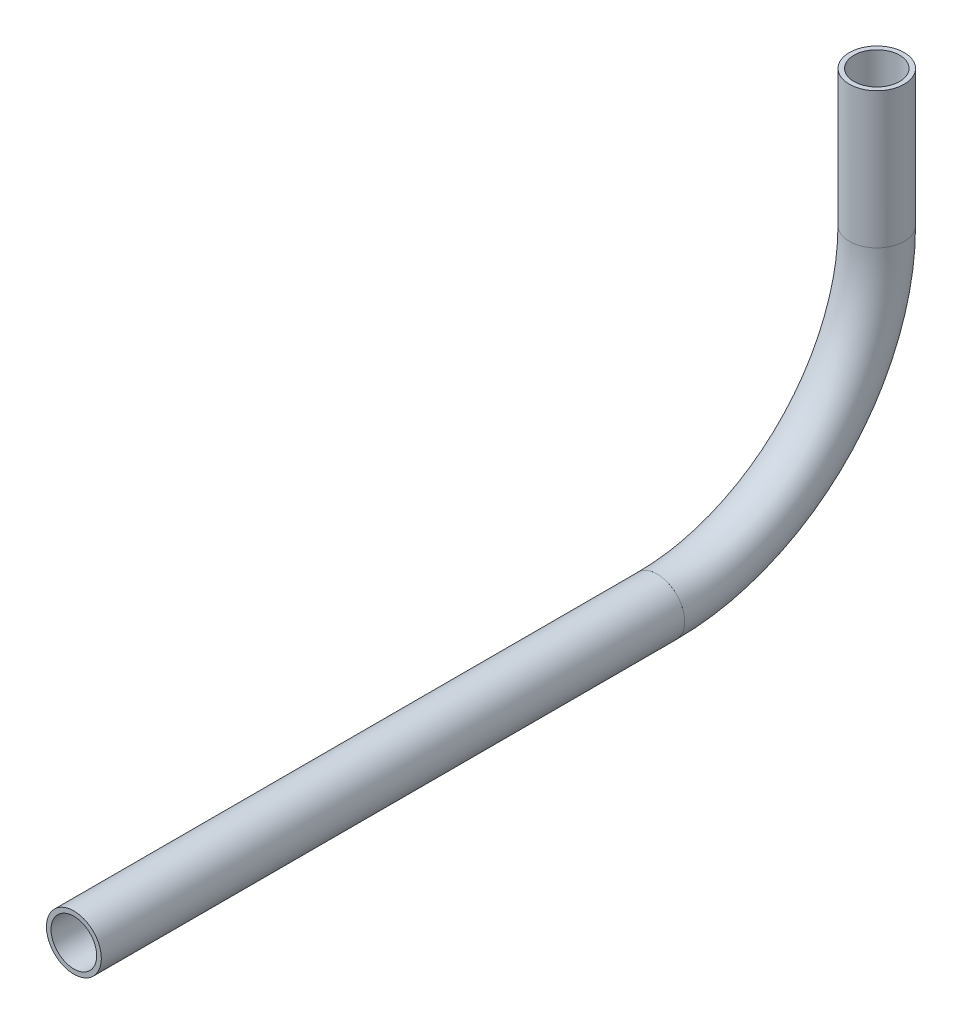
SolidWorks part; units mm, degrees
ref_plane "Front Plane" through (0, 0, 0) normal (0, 0, 1) x (1, 0, 0)
ref_plane "Top Plane" through (0, 0, 0) normal (0, 1, 0) x (1, 0, 0)
ref_plane "Right Plane" through (0, 0, 0) normal (1, 0, 0) x (0, 0, -1)
sketch "Sketch1" plane through (0, 0, 0) normal (1, 0, 0) x (0, 0, -1)
  line L0 (-303.1646, 670.1656) -> (-168.1736, 670.1656)
  line L1 (-117.3736, 720.9656) -> (-117.3736, 752.4586)
  arc A0 (-168.1736, 670.1656) -> (-117.3736, 720.9656) centre (-168.1736, 720.9656) ccw
  point P2 (-117.3736, 720.9656)
  dimension "D1" = 50.8
other "Pipe 0.5 SCH 40(1)"
ref_plane "Plane1" through (0, 670.1656, 303.1646) normal (0, 0, -1) x (0, 1, 0)
sketch "Sketch11" plane through (0, 670.1656, 303.1646) normal (0, 0, -1) x (0, 1, 0)
  circle A0 centre (0, 0) radius 5.2832
  circle A1 centre (0, 0) radius 6.35
  point P5 (0, 0)
  dimension "In_dia" = 10.5664
  dimension "Out_dia" = 12.7
